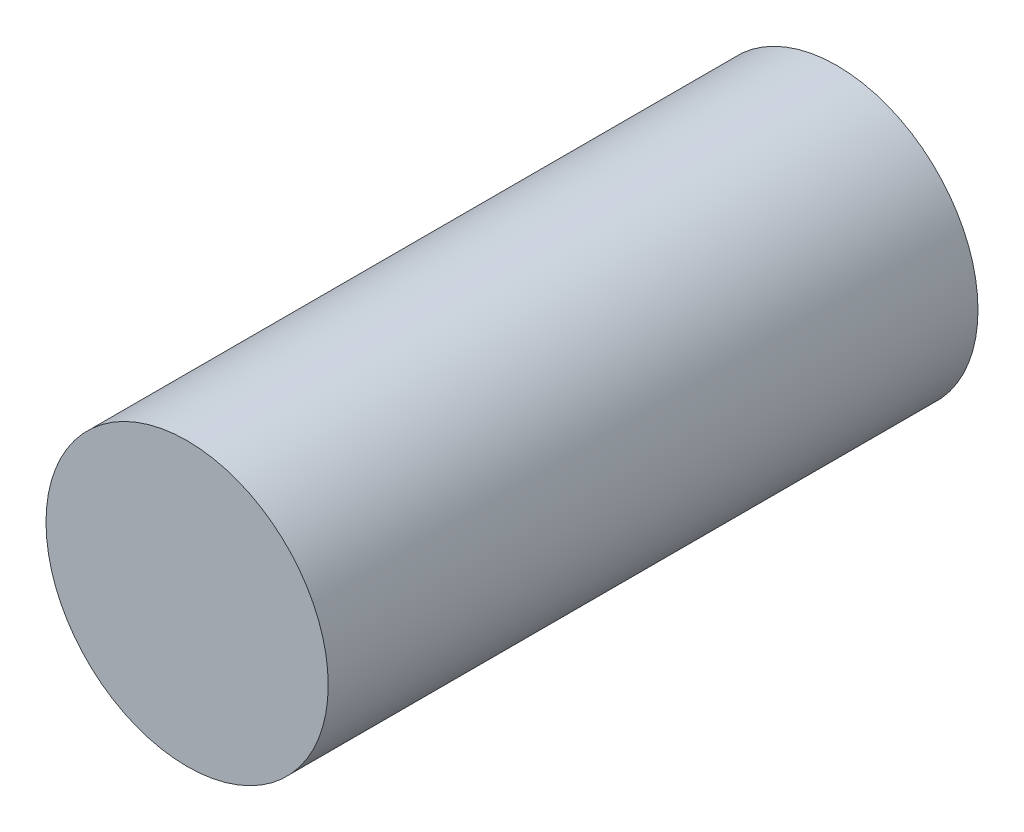
SolidWorks part; units mm, degrees
ref_plane "Alzado" through (0, 0, 0) normal (0, 0, 1) x (1, 0, 0)
ref_plane "Planta" through (0, 0, 0) normal (0, 1, 0) x (1, 0, 0)
ref_plane "Vista lateral" through (0, 0, 0) normal (1, 0, 0) x (0, 0, -1)
sketch "Croquis1" plane through (0, 0, 0) normal (0, 0, 1) x (1, 0, 0)
  circle A0 centre (0, 0) radius 15.2
  dimension "D1" = 30.4
extrude "Saliente-Extruir1" add sketch "Croquis1" along normal blind 70
